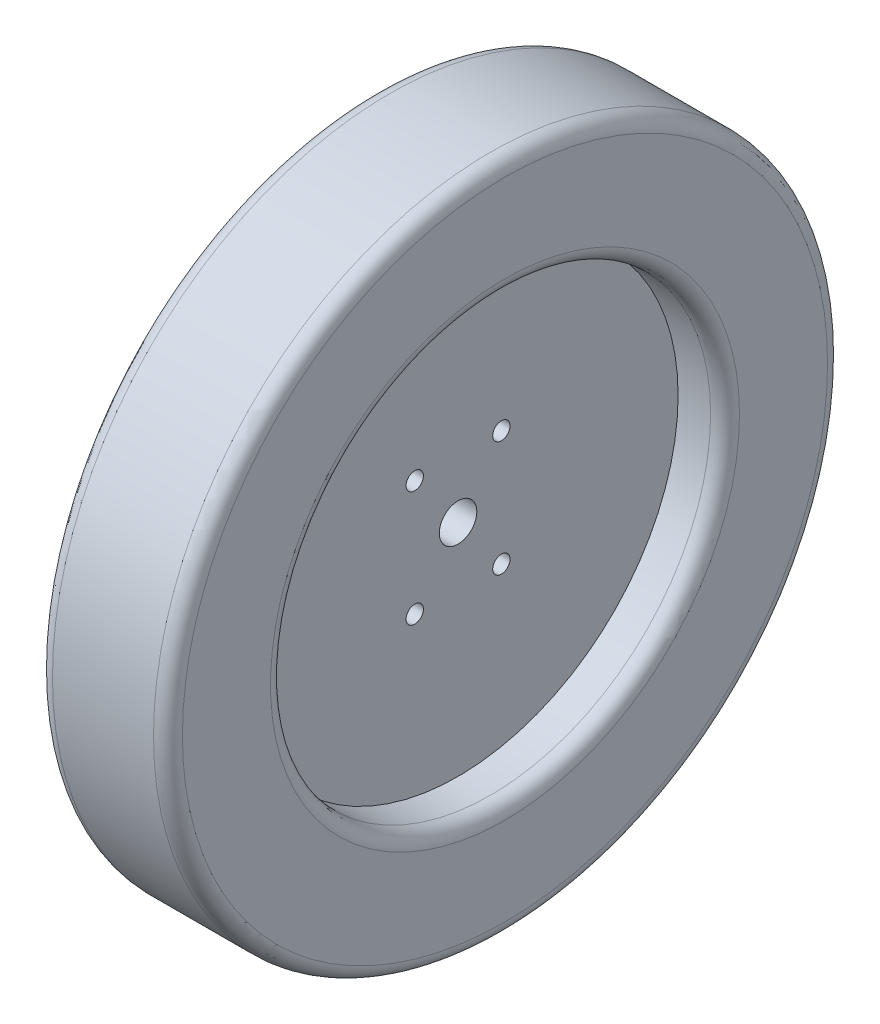
SolidWorks part; units mm, degrees
ref_plane "Front Plane" through (0, 0, 0) normal (0, 0, 1) x (1, 0, 0)
ref_plane "Top Plane" through (0, 0, 0) normal (0, 1, 0) x (1, 0, 0)
ref_plane "Right Plane" through (0, 0, 0) normal (1, 0, 0) x (0, 0, -1)
sketch "Sketch1" plane through (0, 0, 0) normal (1, 0, 0) x (0, 0, -1)
  circle A0 centre (0, 0) radius 152.4
  circle A1 centre (0, 0) radius 233.4
  dimension "D1" = 304.8
  dimension "D2" = 81
extrude "Boss-Extrude1" add sketch "Sketch1" along normal mid plane 90
sketch "Sketch2" plane through (0, 0, 0) normal (1, 0, 0) x (0, 0, -1)
  circle A1 centre (0, 0) radius 233.4
  circle A2 centre (0, 0) radius 233.4
  circle A3 centre (0, 0) radius 152.4
  circle A4 centre (0, 0) radius 152.4
  dimension "D1" = 0
  dimension "D2" = 0
extrude "Boss-Extrude2" add sketch "Sketch2" along normal mid plane 25 contours A4
fillet "Fillet2" radius 10 1 edges at (45, 0, -233.4)
fillet "Fillet3" radius 10 2 edges at (-45, 0, -233.4) (45, 0, -152.4)
fillet "Fillet4" radius 10 1 edges at (-45, 0, -152.4)
sketch "Sketch3" plane through (0, 0, 0) normal (1, 0, 0) x (0, 0, -1)
  line L0 (0, 0) -> (0, 40) construction
  line L1 (0, 40) -> (30, 40) construction
  line L2 (0, 0) -> (26.648, 0) construction
  circle A0 centre (0, 0) radius 13
  circle A1 centre (0, 0) radius 152.4
  circle A2 centre (0, 0) radius 152.4
  circle A3 centre (30, 40) radius 6
  circle A4 centre (-30, 40) radius 6
  circle A5 centre (-30, -40) radius 6
  circle A6 centre (30, -40) radius 6
  dimension "D2" = 26
  dimension "D5" = 12
  dimension "D3" = 40
  dimension "D4" = 30
  dimension "D1" = 0
extrude "Cut-Extrude2" cut sketch "Sketch3" against normal through all both and the other way through all contours A4 | A3 | A0 | A5 | A6
